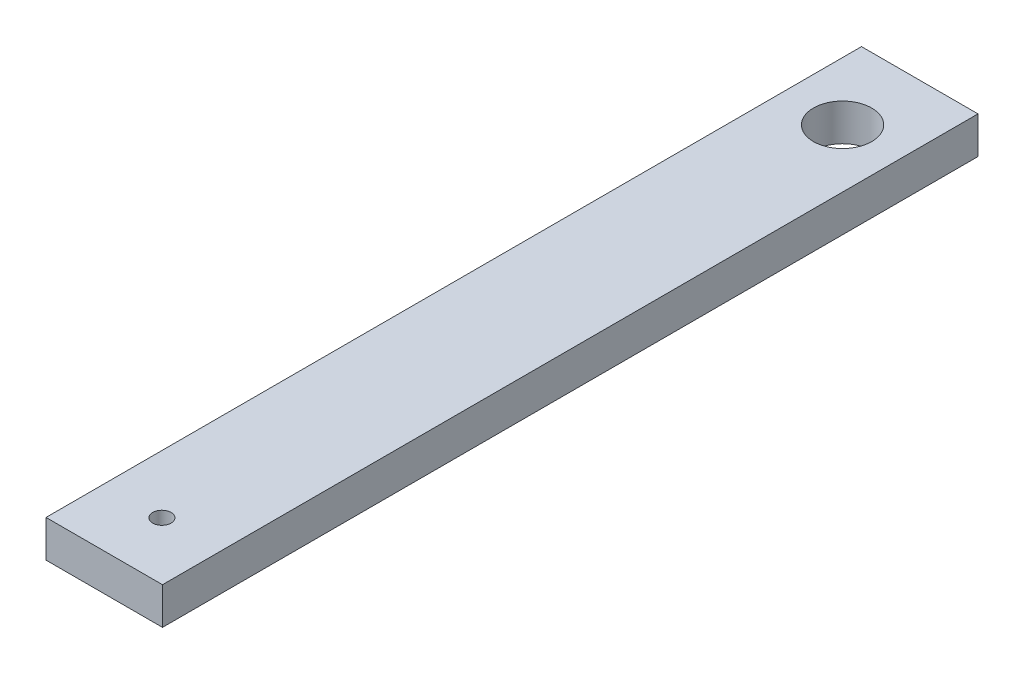
SolidWorks part; units mm, degrees
ref_plane "Front Plane" through (0, 0, 0) normal (0, 0, 1) x (1, 0, 0)
ref_plane "Top Plane" through (0, 0, 0) normal (0, 1, 0) x (1, 0, 0)
ref_plane "Right Plane" through (0, 0, 0) normal (1, 0, 0) x (0, 0, -1)
sketch "Sketch1" plane through (0, 0, 0) normal (0, 1, 0) x (1, 0, 0)
  line L0 (0, -63.375) -> (0, 63.375) construction
  line L1 (-10, -63.375) -> (10, -63.375)
  line L2 (-10, -63.375) -> (-10, 76.625)
  line L3 (-10, 76.625) -> (10, 76.625)
  line L4 (10, -63.375) -> (10, 76.625)
  line L5 (0, -63.375) -> (0, -53.4777) construction
  circle A0 centre (0, 63.375) radius 5
  circle A1 centre (0, -53.4777) radius 1.5875
  point P10 (-10, 6.625)
  point P11 (0, 0)
  point P12 (0, 76.625)
  dimension "D3" = 10
  dimension "D4" = 3.175
  dimension "D5" = 13.25
  dimension "D6" = 9.8973
  dimension "D1" = 20
  dimension "D2" = 140
extrude "Boss-Extrude1" add sketch "Sketch1" along normal blind 6.35
